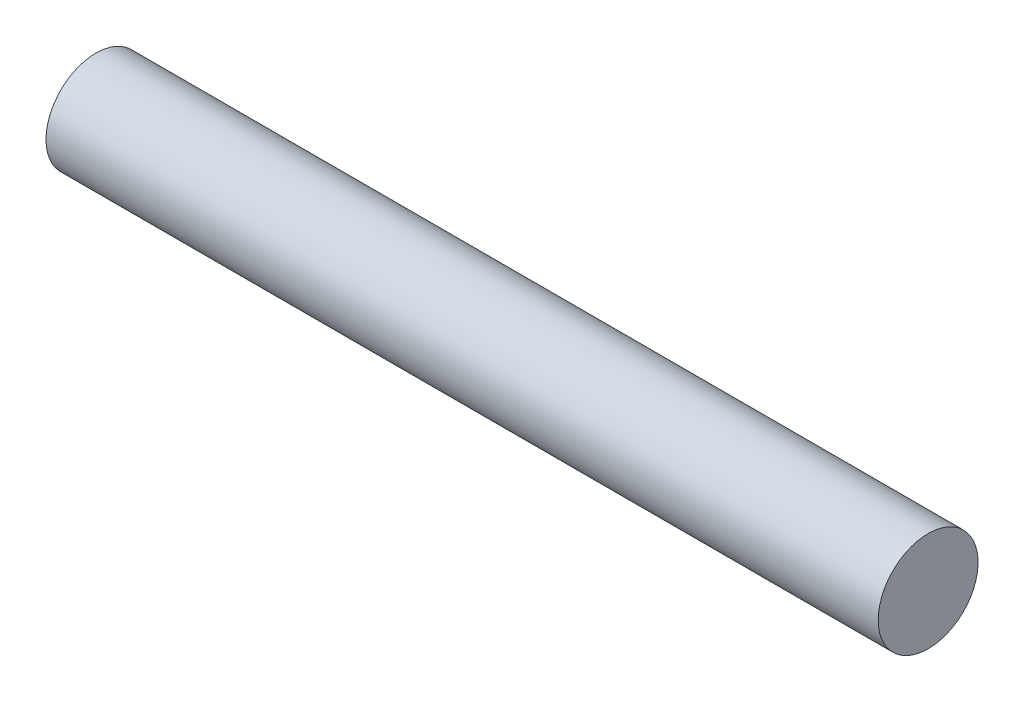
SolidWorks part; units mm, degrees
ref_plane "Front Plane" through (0, 0, 0) normal (0, 0, 1) x (1, 0, 0)
ref_plane "Top Plane" through (0, 0, 0) normal (0, 1, 0) x (1, 0, 0)
ref_plane "Right Plane" through (0, 0, 0) normal (1, 0, 0) x (0, 0, -1)
sketch "Sketch1" plane through (0, 0, 0) normal (0, 1, 0) x (1, 0, 0)
  line L0 (0, 0) -> (258.278, 0) construction
  line L1 (0, 0) -> (0, 12)
  line L2 (0, 12) -> (200, 12)
  line L3 (200, 12) -> (200, 0)
  line L4 (200, 0) -> (0, 0)
  dimension "D1" = 0
  dimension "D2" = 24
  dimension "D3" = 200
revolve "Revolve1" add sketch "Sketch1" angle 360 about L0
